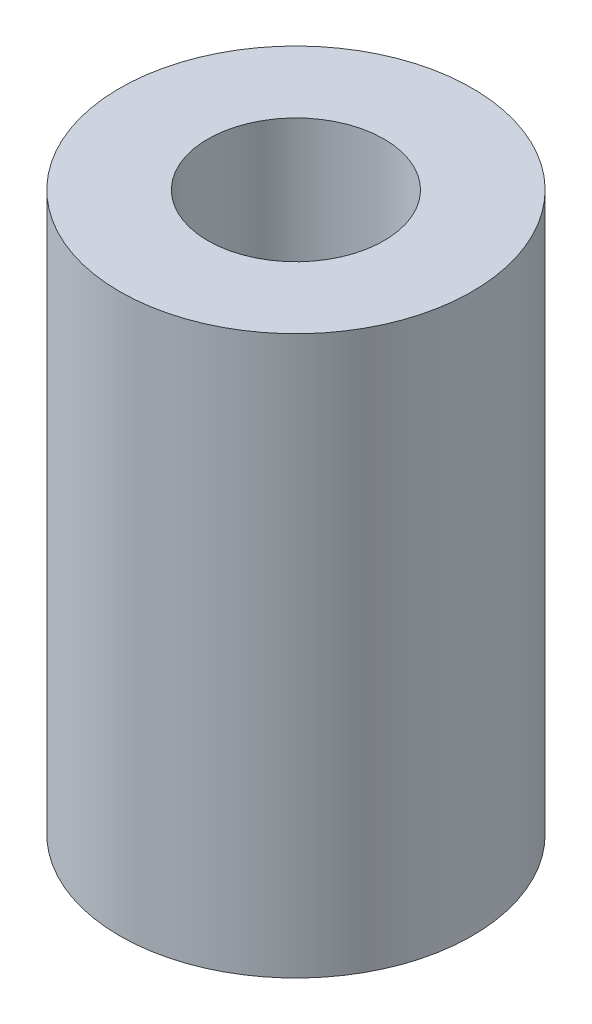
SolidWorks part; units mm, degrees
material "PTFE (general)"
ref_plane "Front Plane" through (0, 0, 0) normal (0, 0, 1) x (1, 0, 0)
ref_plane "Top Plane" through (0, 0, 0) normal (0, 1, 0) x (1, 0, 0)
ref_plane "Right Plane" through (0, 0, 0) normal (1, 0, 0) x (0, 0, -1)
sketch "Sketch1" plane through (0, 0, 0) normal (0, 1, 0) x (1, 0, 0)
  circle A0 centre (0, 0) radius 6
  circle A1 centre (0, 0) radius 3
  dimension "D1" = 6
  dimension "D2" = 12
extrude "Boss-Extrude1" add sketch "Sketch1" along normal blind 19
